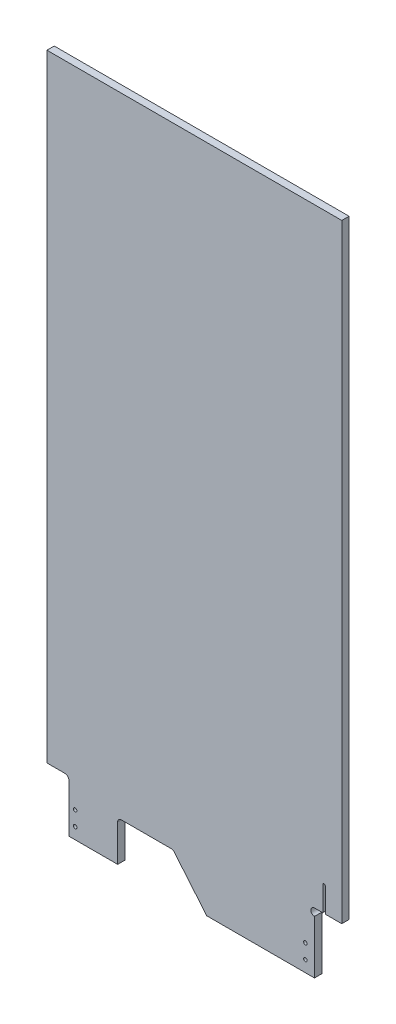
SolidWorks part; units mm, degrees
material "Maple"
ref_plane "Front Plane" through (0, 0, 0) normal (0, 0, 1) x (1, 0, 0)
ref_plane "Top Plane" through (0, 0, 0) normal (0, 1, 0) x (1, 0, 0)
ref_plane "Right Plane" through (0, 0, 0) normal (1, 0, 0) x (0, 0, -1)
sketch "Sketch1" plane through (0, 0, 0) normal (0, 0, 1) x (1, 0, 0)
  line L0 (10736.3381, 13352.0402) -> (10736.3381, 13308.8602)
  line L1 (10731.7661, 13352.0402) -> (10731.7661, 13308.8602)
  line L2 (10778.248, 13352.0402) -> (10778.248, 13308.8602)
  line L3 (10773.676, 13352.0402) -> (10773.676, 13308.8602)
  line L4 (10615.3515, 13397.3654) -> (10620.1422, 13428.7519)
  line L5 (10604.4489, 13431.1472) -> (10599.6582, 13399.7607)
  line L6 (10443.2333, 13331.6551) -> (10455.9847, 13336.0691)
  line L7 (10447.1279, 13320.4039) -> (10459.8794, 13324.8178)
  line L8 (10695.1971, 13320.4039) -> (10682.4456, 13324.8178)
  line L9 (10699.0917, 13331.6551) -> (10686.3403, 13336.0691)
  line L10 (10619.0538, 13432.1426) -> (10606.4992, 13434.0589)
  line L11 (10602.867, 13431.3887) -> (10598.0763, 13400.0022)
  line L12 (10577.5125, 13436.2658) -> (10564.8125, 13436.2724)
  line L13 (10564.7928, 13398.147) -> (10577.4928, 13398.1405)
  line L14 (10645.05, 13422.9934) -> (10635.5783, 13392.6891)
  line L15 (10563.2233, 13433.0855) -> (10563.207, 13401.3355)
  line L16 (10579.082, 13401.3273) -> (10579.0983, 13433.0773)
  line L17 (10482.8792, 13420.2463) -> (10495.0009, 13424.035)
  line L18 (10505.4197, 13390.7003) -> (10493.298, 13386.9116)
  line L19 (10541.0517, 13397.9519) -> (10528.4971, 13396.0356)
  line L20 (10526.6882, 13397.3654) -> (10521.8975, 13428.7519)
  line L21 (10537.5908, 13431.1472) -> (10542.3815, 13399.7607)
  line L22 (10491.3092, 13387.9533) -> (10481.8376, 13418.2575)
  line L23 (10577.5117, 13434.6656) -> (10564.8117, 13434.6722)
  line L24 (10650.7305, 13387.9533) -> (10660.2022, 13418.2575)
  line L25 (10523.2273, 13430.5607) -> (10535.7819, 13432.477)
  line L26 (10522.9859, 13432.1426) -> (10535.5405, 13434.0589)
  line L27 (10482.4018, 13421.7737) -> (10494.5235, 13425.5623)
  line L28 (10498.517, 13423.4707) -> (10507.9887, 13393.1665)
  line L29 (10564.7937, 13399.7472) -> (10577.4937, 13399.7407)
  line L30 (10496.9897, 13422.9934) -> (10506.4614, 13392.6891)
  line L31 (10636.62, 13390.7003) -> (10648.7417, 13386.9116)
  line L32 (10539.1727, 13431.3887) -> (10543.9634, 13400.0022)
  line L33 (10618.8124, 13430.5607) -> (10606.2578, 13432.477)
  line L34 (10600.988, 13397.9519) -> (10613.5426, 13396.0356)
  line L35 (10505.8971, 13389.173) -> (10493.7754, 13385.3843)
  line L36 (10643.5227, 13423.4707) -> (10634.051, 13393.1665)
  line L37 (10659.6379, 13421.7737) -> (10647.5162, 13425.5623)
  line L38 (10600.7466, 13396.37) -> (10613.3012, 13394.4537)
  line L39 (10616.9334, 13397.1239) -> (10621.724, 13428.5104)
  line L40 (10561.6231, 13433.0863) -> (10561.6068, 13401.3363)
  line L41 (10525.1064, 13397.1239) -> (10520.3157, 13428.5104)
  line L42 (10541.2931, 13396.37) -> (10528.7385, 13394.4537)
  line L43 (10489.7819, 13387.4759) -> (10480.3102, 13417.7802)
  line L44 (10659.1605, 13420.2463) -> (10647.0388, 13424.035)
  line L45 (10804.5257, 13110.5905) -> (10804.5257, 13017.5001)
  line L46 (10804.5257, 13123.2905) -> (10852.1507, 13123.2905)
  line L47 (10823.5812, 13165.8355) -> (10823.5812, 13122.6555)
  line L48 (10819.0092, 13165.8355) -> (10819.0092, 13122.6555)
  line L49 (10652.2578, 13387.4759) -> (10661.7295, 13417.7802)
  line L50 (10636.1426, 13389.173) -> (10648.2643, 13385.3843)
  line L51 (10580.6822, 13401.3265) -> (10580.6985, 13433.0765)
  line L52 (10410.6461, 13352.5482) -> (10410.6461, 13309.3682)
  line L53 (10406.0741, 13352.5482) -> (10406.0741, 13309.3682)
  line L54 (10461.2028, 13017.5001) -> (10461.2028, 13081.5947)
  line L55 (10559.6499, 13085.667) -> (10616.6252, 13017.5001)
  line L56 (10467.5528, 13087.9447) -> (10554.7777, 13087.9447)
  line L57 (10604.6398, 13059.119) -> (10650.0487, 13080.9819)
  line L58 (10597.0129, 13060.7681) -> (10579.755, 13081.4159)
  line L59 (10633.2213, 13115.9323) -> (10581.8726, 13091.2096)
  line L60 (10653.0155, 13089.4579) -> (10641.6974, 13112.9655)
  line L61 (10776.2577, 13185.5577) -> (10728.0783, 13162.3608)
  line L62 (10725.8532, 13156.0038) -> (10738.5668, 13129.5979)
  line L63 (10795.3283, 13156.9268) -> (10782.6147, 13183.3327)
  line L64 (10744.9239, 13127.3729) -> (10793.1033, 13150.5697)
  line L65 (10616.6252, 13017.5001) -> (10804.5257, 13017.5001)
  line L66 (10337.8007, 14185.9001) -> (10337.8021, 13109.003)
  line L67 (10852.1479, 14185.9001) -> (10852.1507, 13123.2905)
  line L68 (10337.8007, 14185.9001) -> (10852.1479, 14185.9001)
  line L69 (10375.9021, 13017.5001) -> (10461.2028, 13017.5001)
  line L70 (10375.9021, 13017.5001) -> (10375.9021, 13102.653)
  line L71 (10369.5521, 13109.003) -> (10337.8021, 13109.003)
  line L72 (10368.649, 13352.5482) -> (10368.649, 13309.3682)
  line L73 (10364.077, 13352.5482) -> (10364.077, 13309.3682)
  circle A0 centre (10344.1507, 13550.9001) radius 1.5875
  circle A1 centre (10344.1507, 13703.3001) radius 1.5875
  circle A2 centre (10344.1507, 14008.1001) radius 1.5875
  circle A3 centre (10344.1507, 13855.7001) radius 1.5875
  circle A4 centre (10399.3957, 14179.2527) radius 1.5875
  circle A5 centre (10344.1507, 14160.5001) radius 1.5875
  circle A6 centre (10845.8007, 13550.9001) radius 1.5875
  circle A7 centre (10798.187, 13550.9001) radius 1.5875
  circle A8 centre (10845.8007, 13703.3001) radius 1.5875
  circle A9 centre (10845.8007, 13855.7001) radius 1.5875
  circle A10 centre (10845.8007, 14008.1001) radius 1.5875
  circle A11 centre (10692.7657, 14179.2527) radius 1.5875
  circle A12 centre (10594.9757, 14179.2527) radius 1.5875
  circle A13 centre (10497.1857, 14179.2527) radius 1.5875
  circle A14 centre (10845.7979, 14160.5001) radius 1.5875
  circle A15 centre (10790.5557, 14179.2527) radius 1.5875
  arc A16 (10731.7661, 13308.8602) -> (10736.3381, 13308.8602) centre (10734.0521, 13308.8602) ccw
  arc A17 (10736.3381, 13352.0402) -> (10731.7661, 13352.0402) centre (10734.0521, 13352.0402) ccw
  arc A18 (10773.676, 13308.8602) -> (10778.248, 13308.8602) centre (10775.962, 13308.8602) ccw
  arc A19 (10778.248, 13352.0402) -> (10773.676, 13352.0402) centre (10775.962, 13352.0402) ccw
  circle A20 centre (10571.0813, 13317.8883) radius 12.7381
  circle A21 centre (10571.086, 13282.9633) radius 12.7381
  circle A22 centre (10571.0199, 13218.5702) radius 19.0881
  circle A23 centre (10571.0767, 13352.8133) radius 12.7381
  circle A24 centre (10467.2005, 13279.1384) radius 2.0955
  circle A25 centre (10734.0521, 13398.9488) radius 11.1125
  circle A26 centre (10775.962, 13398.9364) radius 11.1125
  circle A27 centre (10467.9679, 13213.2533) radius 2.0955
  circle A28 centre (10674.3571, 13213.2533) radius 2.0955
  circle A29 centre (10708.3278, 13236.4728) radius 2.0955
  circle A30 centre (10742.2986, 13259.6923) radius 2.0955
  circle A31 centre (10675.1245, 13279.1384) radius 2.0955
  circle A32 centre (10444.8254, 13353.4836) radius 5.9531
  circle A33 centre (10461.8744, 13304.2311) radius 5.9531
  arc A34 (10459.8794, 13324.8178) -> (10455.9847, 13336.0691) centre (10457.932, 13330.4435) ccw
  arc A35 (10443.2333, 13331.6551) -> (10447.1279, 13320.4039) centre (10445.1806, 13326.0295) ccw
  circle A36 centre (10680.4506, 13304.2311) radius 5.9531
  circle A37 centre (10697.4996, 13353.4836) radius 5.9531
  arc A38 (10686.3403, 13336.0691) -> (10682.4456, 13324.8178) centre (10684.393, 13330.4435) ccw
  arc A39 (10695.1971, 13320.4039) -> (10699.0917, 13331.6551) centre (10697.1444, 13326.0295) ccw
  circle A40 centre (10571.0813, 13317.8883) radius 11.1125
  circle A41 centre (10571.086, 13282.9633) radius 11.1125
  arc A42 (10613.3012, 13394.4537) -> (10616.9334, 13397.1239) centre (10613.7821, 13397.6049) ccw
  arc A43 (10606.4992, 13434.0589) -> (10602.867, 13431.3887) centre (10606.0182, 13430.9077) ccw
  arc A44 (10577.4928, 13398.1405) -> (10580.6822, 13401.3265) centre (10577.4945, 13401.3282) ccw
  circle A45 centre (10755.007, 13352.2942) radius 2.0955
  circle A46 centre (10708.8263, 13376.4992) radius 2.0955
  circle A47 centre (10708.8263, 13302.174) radius 2.0955
  arc A48 (10539.1727, 13431.3887) -> (10535.5405, 13434.0589) centre (10536.0215, 13430.9077) ccw
  arc A49 (10541.2931, 13396.37) -> (10543.9634, 13400.0022) centre (10540.8122, 13399.5212) ccw
  arc A50 (10522.9859, 13432.1426) -> (10520.3157, 13428.5104) centre (10523.4669, 13428.9914) ccw
  arc A51 (10505.8971, 13389.173) -> (10507.9887, 13393.1665) centre (10504.9462, 13392.2155) ccw
  circle A52 centre (10775.962, 13398.9364) radius 12.7381
  circle A53 centre (10734.0521, 13398.9488) radius 12.7381
  circle A54 centre (10571.0767, 13352.8133) radius 11.1125
  circle A55 centre (10571.0199, 13218.5702) radius 17.4625
  circle A56 centre (10725.3132, 13248.0825) radius 5.9531
  circle A57 centre (10691.29, 13224.8272) radius 5.9531
  arc A58 (10482.4018, 13421.7737) -> (10480.3102, 13417.7802) centre (10483.3528, 13418.7311) ccw
  arc A59 (10634.051, 13393.1665) -> (10636.1426, 13389.173) centre (10637.0935, 13392.2155) ccw
  arc A60 (10598.0763, 13400.0022) -> (10600.7466, 13396.37) centre (10601.2276, 13399.5212) ccw
  arc A61 (10561.6068, 13401.3363) -> (10564.7928, 13398.147) centre (10564.7945, 13401.3347) ccw
  arc A62 (10525.1064, 13397.1239) -> (10528.7385, 13394.4537) centre (10528.2576, 13397.6049) ccw
  arc A63 (10489.7819, 13387.4759) -> (10493.7754, 13385.3843) centre (10492.8244, 13388.4268) ccw
  arc A64 (10661.7295, 13417.7802) -> (10659.6379, 13421.7737) centre (10658.6869, 13418.7311) ccw
  circle A65 centre (10665.5741, 13083.9291) radius 2.159
  circle A66 centre (10644.7487, 13126.7595) radius 2.159
  circle A67 centre (10713.2773, 13160.0802) radius 2.159
  circle A68 centre (10747.5416, 13176.7405) radius 2.159
  circle A69 centre (10793.7362, 13135.3438) radius 1.1303
  arc A70 (10823.5812, 13165.8355) -> (10819.0092, 13165.8355) centre (10821.2952, 13165.8355) ccw
  arc A71 (10819.0092, 13122.6555) -> (10823.5812, 13122.6555) centre (10821.2952, 13122.6555) ccw
  circle A72 centre (10488.1149, 13199.4826) radius 6.35
  circle A73 centre (10654.2101, 13199.4826) radius 6.35
  circle A74 centre (10755.007, 13368.1412) radius 3.1115
  circle A75 centre (10845.8007, 13246.1001) radius 1.5875
  circle A76 centre (10796.8058, 13309.9208) radius 1.5875
  circle A77 centre (10796.8058, 13247.433) radius 1.5875
  circle A78 centre (10691.9754, 13290.6562) radius 5.9531
  circle A79 centre (10708.8263, 13339.3366) radius 5.9531
  circle A80 centre (10845.8007, 13398.5001) radius 1.5875
  circle A81 centre (10798.187, 13398.5001) radius 1.5875
  arc A82 (10648.2643, 13385.3843) -> (10652.2578, 13387.4759) centre (10649.2153, 13388.4268) ccw
  arc A83 (10621.724, 13428.5104) -> (10619.0538, 13432.1426) centre (10618.5728, 13428.9914) ccw
  arc A84 (10580.6985, 13433.0765) -> (10577.5125, 13436.2658) centre (10577.5108, 13433.0781) ccw
  arc A85 (10406.0741, 13309.3682) -> (10410.6461, 13309.3682) centre (10408.3601, 13309.3682) ccw
  arc A86 (10410.6461, 13352.5482) -> (10406.0741, 13352.5482) centre (10408.3601, 13352.5482) ccw
  circle A87 centre (10433.4987, 13376.4992) radius 2.0955
  circle A88 centre (10433.4987, 13302.174) radius 2.0955
  circle A89 centre (10387.318, 13352.2942) radius 2.0955
  circle A90 centre (10400.0264, 13259.6923) radius 2.0955
  circle A91 centre (10433.9972, 13236.4728) radius 2.0955
  arc A92 (10559.6499, 13085.667) -> (10554.7777, 13087.9447) centre (10554.7777, 13081.5947) ccw
  arc A93 (10467.5528, 13087.9447) -> (10461.2028, 13081.5947) centre (10467.5528, 13081.5947) ccw
  arc A94 (10597.0129, 13060.7681) -> (10604.6398, 13059.119) centre (10601.8851, 13064.8404) ccw
  arc A95 (10581.8726, 13091.2096) -> (10579.755, 13081.4159) centre (10584.6273, 13085.4882) ccw
  arc A96 (10650.0487, 13080.9819) -> (10653.0155, 13089.4579) centre (10647.2941, 13086.7033) ccw
  arc A97 (10641.6974, 13112.9655) -> (10633.2213, 13115.9323) centre (10635.976, 13110.2109) ccw
  arc A98 (10728.0783, 13162.3608) -> (10725.8532, 13156.0038) centre (10730.1443, 13158.0698) ccw
  arc A99 (10793.1033, 13150.5697) -> (10795.3283, 13156.9268) centre (10791.0373, 13154.8608) ccw
  arc A100 (10782.6147, 13183.3327) -> (10776.2577, 13185.5577) centre (10778.3237, 13181.2667) ccw
  arc A101 (10738.5668, 13129.5979) -> (10744.9239, 13127.3729) centre (10742.8579, 13131.6639) ccw
  circle A102 centre (10793.7362, 13135.3438) radius 1.1303
  circle A103 centre (10781.6651, 13097.6371) radius 3.1115
  circle A104 centre (10845.8007, 13147.103) radius 1.5875
  arc A105 (10804.5257, 13123.2905) -> (10804.5257, 13110.5905) centre (10804.5257, 13116.9405) ccw
  circle A106 centre (10788.6501, 13037.3121) radius 3.1115
  circle A107 centre (10788.6501, 13062.7121) radius 3.1115
  circle A108 centre (10387.0126, 13062.7121) radius 3.1115
  circle A109 centre (10387.0126, 13037.3121) radius 3.1115
  circle A110 centre (10391.7751, 13097.6371) radius 3.1115
  arc A111 (10375.9021, 13102.653) -> (10369.5521, 13109.003) centre (10369.5521, 13102.653) ccw
  circle A112 centre (10344.1521, 13147.103) radius 1.5875
  circle A113 centre (10387.318, 13368.1412) radius 3.1115
  circle A114 centre (10344.1507, 13398.5001) radius 1.5875
  circle A115 centre (10344.1507, 13246.1001) radius 1.5875
  circle A116 centre (10450.3496, 13290.6562) radius 5.9531
  circle A117 centre (10433.4987, 13339.3366) radius 5.9531
  circle A118 centre (10417.0118, 13248.0825) radius 5.9531
  circle A119 centre (10451.035, 13224.8272) radius 5.9531
  circle A120 centre (10366.363, 13399.1466) radius 12.7381
  circle A121 centre (10408.3601, 13399.1233) radius 12.7381
  circle A122 centre (10408.3601, 13399.1233) radius 11.1125
  circle A123 centre (10366.363, 13399.1466) radius 11.1125
  arc A124 (10364.077, 13309.3682) -> (10368.649, 13309.3682) centre (10366.363, 13309.3682) ccw
  arc A125 (10368.649, 13352.5482) -> (10364.077, 13352.5482) centre (10366.363, 13352.5482) ccw
  ellipse E0 centre (10540.8122, 13399.5212) end of major axis (10541.0517, 13397.9519) minor radius 1.5875 (10541.0517, 13397.9519) -> (10542.3815, 13399.7607) ccw
  ellipse E1 centre (10528.2576, 13397.6049) end of major axis (10528.018, 13399.1742) minor radius 1.5875 (10526.6882, 13397.3654) -> (10528.4971, 13396.0356) ccw
  ellipse E2 centre (10618.5728, 13428.9914) end of major axis (10618.8124, 13430.5607) minor radius 1.5875 (10620.1422, 13428.7519) -> (10618.8124, 13430.5607) ccw
  ellipse E3 centre (10601.2276, 13399.5212) end of major axis (10600.988, 13397.9519) minor radius 1.5875 (10599.6582, 13399.7607) -> (10600.988, 13397.9519) ccw
  ellipse E4 centre (10606.0182, 13430.9077) end of major axis (10604.4489, 13431.1472) minor radius 1.5875 (10606.2578, 13432.477) -> (10604.4489, 13431.1472) ccw
  ellipse E5 centre (10613.7821, 13397.6049) end of major axis (10614.0217, 13399.1742) minor radius 1.5875 (10613.5426, 13396.0356) -> (10615.3515, 13397.3654) ccw
  ellipse E6 centre (10483.3528, 13418.7311) end of major axis (10482.8792, 13420.2463) minor radius 1.5875 (10482.8792, 13420.2463) -> (10481.8376, 13418.2575) ccw
  ellipse E7 centre (10637.0935, 13392.2155) end of major axis (10636.62, 13390.7003) minor radius 1.5875 (10635.5783, 13392.6891) -> (10636.62, 13390.7003) ccw
  ellipse E8 centre (10536.0215, 13430.9077) end of major axis (10537.5908, 13431.1472) minor radius 1.5875 (10537.5908, 13431.1472) -> (10535.7819, 13432.477) ccw
  ellipse E9 centre (10523.4669, 13428.9914) end of major axis (10523.2273, 13430.5607) minor radius 1.5875 (10523.2273, 13430.5607) -> (10521.8975, 13428.7519) ccw
  ellipse E10 centre (10495.4745, 13422.5198) end of major axis (10496.9897, 13422.9934) minor radius 1.5875 (10496.9897, 13422.9934) -> (10495.0009, 13424.035) ccw
  ellipse E11 centre (10564.8108, 13433.0847) end of major axis (10563.2233, 13433.0855) minor radius 1.5875 (10564.8117, 13434.6722) -> (10563.2233, 13433.0855) ccw
  ellipse E12 centre (10658.6869, 13418.7311) end of major axis (10659.1605, 13420.2463) minor radius 1.5875 (10660.2022, 13418.2575) -> (10659.1605, 13420.2463) ccw
  ellipse E13 centre (10577.5108, 13433.0781) end of major axis (10577.5117, 13434.6656) minor radius 1.5875 (10579.0983, 13433.0773) -> (10577.5117, 13434.6656) ccw
  ellipse E14 centre (10564.7945, 13401.3347) end of major axis (10564.7937, 13399.7472) minor radius 1.5875 (10563.207, 13401.3355) -> (10564.7937, 13399.7472) ccw
  ellipse E15 centre (10492.8244, 13388.4268) end of major axis (10492.3509, 13389.942) minor radius 1.5875 (10491.3092, 13387.9533) -> (10493.298, 13386.9116) ccw
  ellipse E16 centre (10649.2153, 13388.4268) end of major axis (10649.6888, 13389.942) minor radius 1.5875 (10648.7417, 13386.9116) -> (10650.7305, 13387.9533) ccw
  ellipse E17 centre (10646.5652, 13422.5198) end of major axis (10645.05, 13422.9934) minor radius 1.5875 (10647.0388, 13424.035) -> (10645.05, 13422.9934) ccw
  ellipse E18 centre (10577.4945, 13401.3282) end of major axis (10577.4953, 13402.9157) minor radius 1.5875 (10577.4937, 13399.7407) -> (10579.082, 13401.3273) ccw
  ellipse E19 centre (10504.9462, 13392.2155) end of major axis (10505.4197, 13390.7003) minor radius 1.5875 (10505.4197, 13390.7003) -> (10506.4614, 13392.6891) ccw
  ellipse E20 centre (10734.1028, 13117.2498) end of major axis (10731.9463, 13117.3544) minor radius 2.159
  ellipse E21 centre (10768.3671, 13133.9102) end of major axis (10766.2106, 13134.0147) minor radius 2.159
  ellipse E22 centre (10623.9467, 13116.645) end of major axis (10622.362, 13116.7419) minor radius 1.5877
  ellipse E23 centre (10599.0864, 13051.6008) end of major axis (10597.5017, 13051.6977) minor radius 1.5877
  ellipse E24 centre (10644.7722, 13073.8146) end of major axis (10643.1875, 13073.9115) minor radius 1.5877
  ellipse E25 centre (10669.6325, 13138.8588) end of major axis (10669.7294, 13140.4435) minor radius 1.5877
  spline S0 degree 3 poles (10564.8125, 13436.2724) (10563.951, 13436.0717) (10562.228, 13435.6702) (10561.8248, 13433.9476) (10561.6231, 13433.0863) knots 0 0 0 0 0.5 1 1 1 1
  spline S1 degree 3 poles (10494.5235, 13425.5623) (10495.4057, 13425.6273) (10497.1701, 13425.7572) (10498.068, 13424.2329) (10498.517, 13423.4707) knots 0 0 0 0 0.5 1 1 1 1
  spline S2 degree 3 poles (10647.5162, 13425.5623) (10646.634, 13425.6273) (10644.8697, 13425.7572) (10643.9717, 13424.2329) (10643.5227, 13423.4707) knots 0 0 0 0 0.5 1 1 1 1
sketch "Sketch2" plane through (0, 0, 0) normal (0, 0, 1) x (1, 0, 0)
  line L0 (10375.9021, 13017.5001) -> (10375.9021, 13102.653)
  line L1 (10369.5521, 13109.003) -> (10337.8021, 13109.003)
  line L2 (10337.8021, 13109.003) -> (10337.8007, 14185.9001)
  line L3 (10337.8007, 14185.9001) -> (10852.1479, 14185.9001)
  line L4 (10852.1479, 14185.9001) -> (10852.1507, 13123.2905)
  line L5 (10852.1507, 13123.2905) -> (10823.5812, 13123.2905)
  line L6 (10804.5257, 13123.2905) -> (10852.1507, 13123.2905) construction
  line L7 (10823.5812, 13165.8355) -> (10823.5812, 13122.6555) construction
  line L8 (10823.5812, 13123.2905) -> (10823.5812, 13165.8355)
  line L9 (10819.0092, 13165.8355) -> (10819.0092, 13123.2905)
  line L10 (10819.0092, 13123.2905) -> (10804.5257, 13123.2905)
  line L11 (10804.5257, 13110.5905) -> (10804.5257, 13017.5001)
  line L12 (10804.5257, 13017.5001) -> (10616.6252, 13017.5001)
  line L13 (10616.6252, 13017.5001) -> (10559.6499, 13085.667)
  line L14 (10554.7777, 13087.9447) -> (10467.5528, 13087.9447)
  line L15 (10461.2028, 13081.5947) -> (10461.2028, 13017.5001)
  line L16 (10461.2028, 13017.5001) -> (10375.9021, 13017.5001)
  arc A0 (10375.9021, 13102.653) -> (10369.5521, 13109.003) centre (10369.5521, 13102.653) ccw
  arc A1 (10823.5812, 13165.8355) -> (10819.0092, 13165.8355) centre (10821.2952, 13165.8355) ccw
  arc A2 (10804.5257, 13123.2905) -> (10804.5257, 13110.5905) centre (10804.5257, 13116.9405) ccw
  arc A3 (10559.6499, 13085.667) -> (10554.7777, 13087.9447) centre (10554.7777, 13081.5947) ccw
  arc A4 (10467.5528, 13087.9447) -> (10461.2028, 13081.5947) centre (10467.5528, 13081.5947) ccw
extrude "Extrude1" add sketch "Sketch2" against normal blind 12.7
sketch "Sketch3" plane through (0, 0, 0) normal (0, 0, 1) x (1, 0, 0)
  circle A0 centre (10387.0126, 13062.7121) radius 3.1115
  circle A1 centre (10387.0126, 13037.3121) radius 3.1115
  circle A2 centre (10788.6501, 13062.7121) radius 3.1115
  circle A3 centre (10788.6501, 13037.3121) radius 3.1115
extrude "Cut-Extrude1" cut sketch "Sketch3" against normal up to surface (12.7 mm away) up to face at (10615.7465, 13202.3246, -12.7)
